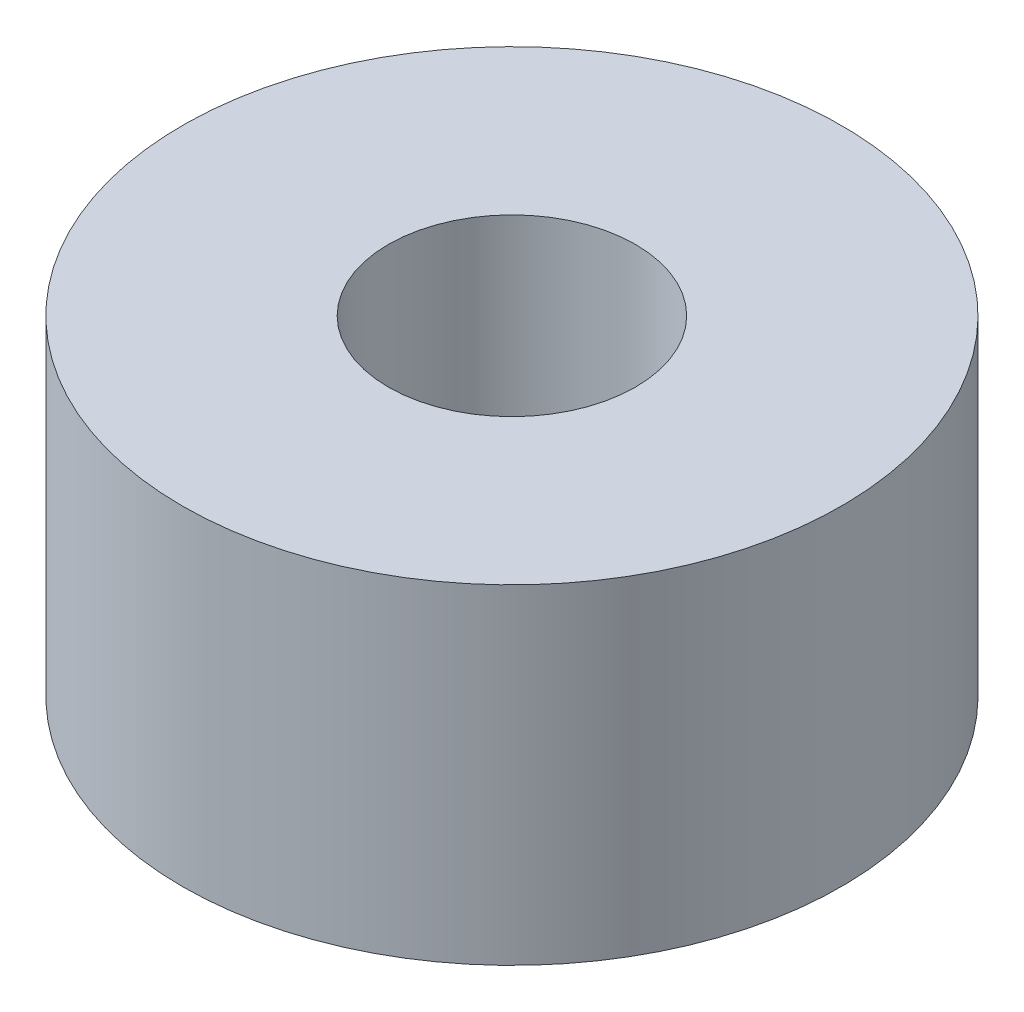
SolidWorks part; units mm, degrees
ref_plane "Front Plane" through (0, 0, 0) normal (0, 0, 1) x (1, 0, 0)
ref_plane "Top Plane" through (0, 0, 0) normal (0, 1, 0) x (1, 0, 0)
ref_plane "Right Plane" through (0, 0, 0) normal (1, 0, 0) x (0, 0, -1)
sketch "Sketch1" plane through (0, 0, 0) normal (0, 1, 0) x (1, 0, 0)
  line L0 (0, -171.7657) -> (0, 8416.5203) construction
  line L1 (-171.7657, 0) -> (8416.5203, 0) construction
  circle A0 centre (0, 0) radius 10
  dimension "D1" = 20
extrude "Boss-Extrude1" add sketch "Sketch1" along normal blind 10
sketch "Sketch2" plane through (0, 10, 0) normal (0, 1, 0) x (1, 0, 0)
  circle A0 centre (0, 0) radius 3.75
  dimension "D1" = 7.5
extrude "Cut-Extrude1" cut sketch "Sketch2" against normal through all both and the other way through all
